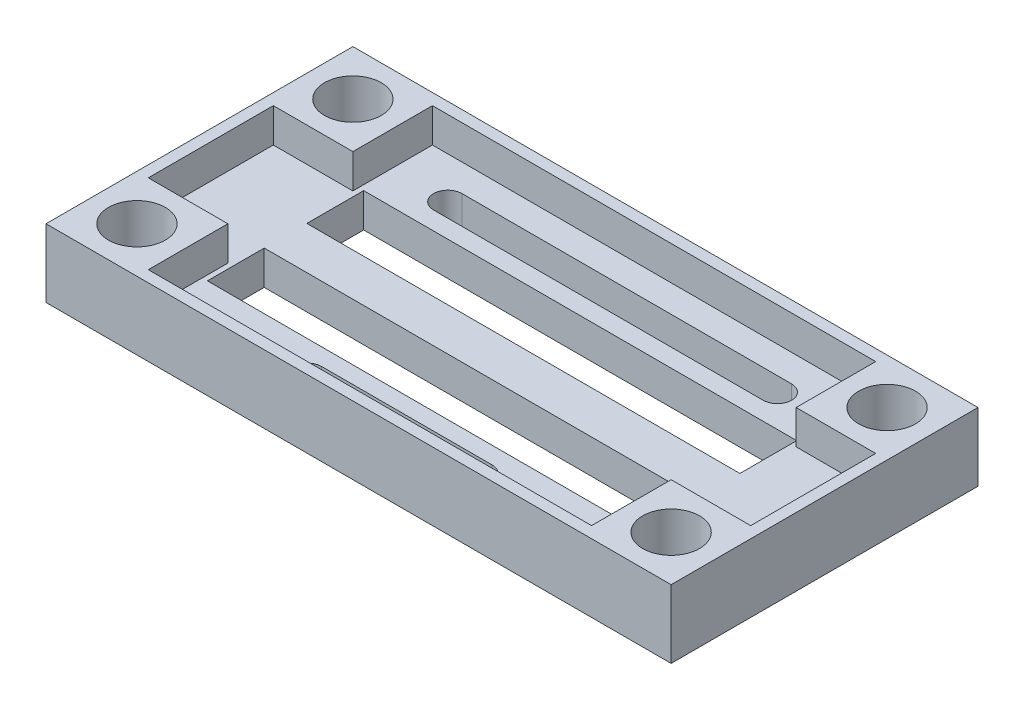
SolidWorks part; units mm, degrees
ref_plane "Front Plane" through (0, 0, 0) normal (0, 0, 1) x (1, 0, 0)
ref_plane "Top Plane" through (0, 0, 0) normal (0, 1, 0) x (1, 0, 0)
ref_plane "Right Plane" through (0, 0, 0) normal (1, 0, 0) x (0, 0, -1)
sketch "Sketch1" plane through (0, 0, 0) normal (0, 1, 0) x (1, 0, 0)
  line L0 (-19.05, -2.75) -> (19.05, -2.75)
  line L9 (27.5, -13.5) -> (-27.5, -13.5)
  line L10 (27.5, -13.5) -> (27.5, 13.5)
  line L11 (27.5, 13.5) -> (-27.5, 13.5)
  line L20 (-27.5, -13.5) -> (-27.5, 13.5)
  line L21 (27.5, -13.5) -> (-27.5, 13.5) construction
  line L22 (27.5, 13.5) -> (-27.5, -13.5) construction
  line L23 (-19.05, 6) -> (19.05, 6)
  line L24 (-19.05, 6) -> (-19.05, 1)
  line L25 (-19.05, 1) -> (19.05, 1)
  line L26 (19.05, 6) -> (19.05, 1)
  line L27 (-19.05, -2.75) -> (-19.05, -7.75)
  line L28 (-19.05, -7.75) -> (19.05, -7.75)
  line L29 (19.05, -2.75) -> (19.05, -7.75)
  point P0 (0, 0)
  point P10 (0, 6)
  point P11 (0, 13.5)
  point P15 (0, -2.75)
  dimension "D2" = 55
  dimension "D1" = 27
  dimension "D3" = 38.1
  dimension "D4" = 7.5
  dimension "D5" = 5
  dimension "D6" = 3.75
extrude "Bottom Base" add sketch "Sketch1" along normal blind 3
sketch "Sketch3" plane through (0, 3, 0) normal (0, 1, 0) x (1, 0, 0)
  line L0 (-27.5, 8.85) -> (27.5, 8.85) construction
  line L1 (27.5, 13.5) -> (-27.5, 13.5) construction
  line L3 (-14.5, 10.1) -> (14.5, 10.1) construction
  line L4 (19.05, 6) -> (-19.05, 6) construction
  line L5 (-14.5, 8.85) -> (14.5, 8.85) construction
  line L6 (-14.5, 10.1) -> (14.5, 10.1)
  line L7 (-14.5, 7.6) -> (14.5, 7.6)
  line L8 (-27.5, 13.5) -> (-27.5, -13.5) construction
  line L9 (27.5, -13.5) -> (27.5, 13.5) construction
  circle A0 centre (-14.5, 8.85) radius 1.09 construction
  circle A2 centre (-14.5, 8.85) radius 1.25 construction
  circle A3 centre (14.5, 8.85) radius 1.25 construction
  arc A6 (-14.5, 10.1) -> (-14.5, 7.6) centre (-14.5, 8.85) ccw
  arc A7 (14.5, 7.6) -> (14.5, 10.1) centre (14.5, 8.85) ccw
  point P21 (0, 6)
  point P22 (0, 10.1)
  point P25 (0, 8.85)
  dimension "D2" = 2.5
  dimension "D5" = 1.25
  dimension "D1" = 29
  dimension "D6" = 4.65
extrude "Sensor Mounting Holes" cut sketch "Sketch3" against normal blind 3
sketch "Sketch4" plane through (0, 3, 0) normal (0, 1, 0) x (1, 0, 0)
  line L0 (27.5, -13.5) -> (27.5, 13.5) construction
  line L1 (27.5, 13.5) -> (-27.5, 13.5) construction
  line L2 (-27.5, -13.5) -> (27.5, -13.5) construction
  line L3 (-27.5, 13.5) -> (-27.5, -13.5) construction
  line L4 (27.5, -13.5) -> (27.5, 13.5)
  line L5 (27.5, 13.5) -> (-27.5, 13.5)
  line L6 (-27.5, -13.5) -> (27.5, -13.5)
  line L7 (-27.5, 13.5) -> (-27.5, -13.5)
  line L8 (26.5, -12.5) -> (26.5, 12.5)
  line L9 (26.5, 12.5) -> (-26.5, 12.5)
  line L10 (-26.5, 12.5) -> (-26.5, -12.5)
  line L11 (-26.5, -12.5) -> (26.5, -12.5)
  line L12 (0, -13.5) -> (0, 13.5) construction
  line L13 (-26.5, -12.5) -> (-19.5, -12.5)
  line L14 (-26.5, -12.5) -> (-26.5, -5.5)
  line L15 (-26.5, -5.5) -> (-19.5, -5.5)
  line L16 (-19.5, -12.5) -> (-19.5, -5.5)
  line L29 (27.5, 0) -> (-27.5, 0) construction
  line L30 (26.5, -5.5) -> (19.5, -5.5)
  line L31 (19.5, -12.5) -> (19.5, -5.5)
  line L32 (26.5, -12.5) -> (19.5, -12.5)
  line L33 (26.5, -12.5) -> (26.5, -5.5)
  line L34 (26.5, 12.5) -> (19.5, 12.5)
  line L35 (19.5, 12.5) -> (19.5, 5.5)
  line L36 (26.5, 5.5) -> (19.5, 5.5)
  line L37 (26.5, 12.5) -> (26.5, 5.5)
  line L38 (-26.5, 5.5) -> (-19.5, 5.5)
  line L39 (-19.5, 12.5) -> (-19.5, 5.5)
  line L40 (-26.5, 12.5) -> (-19.5, 12.5)
  line L41 (-26.5, 12.5) -> (-26.5, 5.5)
  point P14 (0, 0)
  point P17 (0, 0)
  line M13 (-27.5, 13.5) -> (-27.5, -13.5)
  line M14 (-27.5, -13.5) -> (27.5, -13.5)
  line M15 (27.5, -13.5) -> (27.5, 13.5)
  line M16 (27.5, 13.5) -> (-27.5, 13.5)
  dimension "D2" = 7
  dimension "D1" = 1
extrude "Outer Rim" add sketch "Sketch4" along normal blind 3 contours L39 L9 L10 L38 | L11 L16 L15 L10 | L31 L11 L8 L30 | L36 L8 L9 L35 | L11 L10 L9 L8 M16 M13 M14 M15
sketch "Sketch6" plane through (0, 6, 0) normal (0, 1, 0) x (1, 0, 0)
  line L0 (-26.5, -5.5) -> (-19.5, -5.5) construction
  line L1 (-19.5, 5.5) -> (-27.5, 5.5) construction
  line L2 (-19.5, 5.5) -> (-19.5, 13.5) construction
  line L3 (-19.5, 13.5) -> (-27.5, 13.5) construction
  line L4 (-27.5, 5.5) -> (-27.5, 13.5) construction
  line L5 (-19.5, 5.5) -> (-27.5, 13.5) construction
  line L6 (-19.5, 13.5) -> (-27.5, 5.5) construction
  line L7 (-19.5, -13.5) -> (-27.5, -13.5) construction
  line L8 (-19.5, -13.5) -> (-19.5, -5.5) construction
  line L9 (-19.5, -5.5) -> (-27.5, -5.5) construction
  line L10 (-27.5, -13.5) -> (-27.5, -5.5) construction
  line L11 (-19.5, -13.5) -> (-27.5, -5.5) construction
  line L12 (-19.5, -5.5) -> (-27.5, -13.5) construction
  line L17 (-26.5, -5.5) -> (-19.5, -5.5) construction
  line L18 (19.5, -12.5) -> (19.5, -5.5) construction
  line L23 (27.5, 5.5) -> (19.5, 5.5) construction
  line L24 (27.5, 5.5) -> (27.5, 13.5) construction
  line L25 (27.5, 13.5) -> (19.5, 13.5) construction
  line L26 (19.5, 5.5) -> (19.5, 13.5) construction
  line L27 (27.5, 5.5) -> (19.5, 13.5) construction
  line L28 (27.5, 13.5) -> (19.5, 5.5) construction
  line L29 (27.5, -13.5) -> (19.5, -13.5) construction
  line L30 (27.5, -13.5) -> (27.5, -5.5) construction
  line L31 (27.5, -5.5) -> (19.5, -5.5) construction
  line L32 (19.5, -13.5) -> (19.5, -5.5) construction
  line L33 (27.5, -13.5) -> (19.5, -5.5) construction
  line L34 (27.5, -5.5) -> (19.5, -13.5) construction
  line L35 (-19.5, -12.5) -> (-19.5, -5.5) construction
  line L36 (-19.5, -12.5) -> (-19.5, -5.5) construction
  line L37 (27.5, -13.5) -> (27.5, 13.5) construction
  point P0 (-23.5, 9.5)
  point P5 (-23.5, -9.5)
  point P10 (23.5, -9.5)
  point P16 (23.5, 9.5)
hole_wizard "M4 bolt holes" positions "Sketch7" profile "Sketch8" hole size "Ø5.0" standard "ANSI Metric" end condition through all
sketch "Sketch7" plane through (0, 6, 0) normal (0, 1, 0) x (1, 0, 0)
  line L0 (-19.5, -13.5) -> (-27.5, -5.5) construction
  point P0 (-23.5, 9.5)
  point P3 (-23.5, -9.5)
  point P7 (23.5, 9.5)
  point P10 (23.5, -9.5)
sketch "Sketch8" plane through (-23.5, 6, -9.5) normal (1, 0, 0) x (0, 0, 1)
  line L0 (0, 0) -> (0, 6)
  line L1 (0, 6) -> (2.5, 6)
  line L2 (2.5, 6) -> (2.5, 0)
  line L5 (2.5, 0) -> (0, 0)
  line L11 (0, -6.35) -> (0, 107.95) construction
  dimension "Thru Hole Dia." = 5
  dimension "Thru Hole Depth" = 6
sketch "Sketch10" plane through (0, 0, 0) normal (0, -1, 0) x (1, 0, 0)
  line L0 (-27.5, -3.5) -> (27.5, -3.5) construction
  line L1 (-27.5, -13.5) -> (-27.5, 13.5) construction
  line L2 (27.5, 13.5) -> (27.5, -13.5) construction
  line L3 (-19.05, -6) -> (-19.05, -1) construction
  point P8 (-19.05, -3.5)
sketch "Sketch11" plane through (0, 3, 0) normal (0, 1, 0) x (1, 0, 0)
  line L0 (-7.5, -10.5) -> (7.5, -10.5) construction
  line L1 (-7.5, -9.25) -> (7.5, -9.25)
  line L2 (-7.5, -11.75) -> (7.5, -11.75)
  line L3 (-19.5, -12.5) -> (19.5, -12.5) construction
  arc A0 (-7.5, -9.25) -> (-7.5, -11.75) centre (-7.5, -10.5) ccw
  arc A1 (7.5, -11.75) -> (7.5, -9.25) centre (7.5, -10.5) ccw
  arc A2 (-14.5, 10.1) -> (-14.5, 7.6) centre (-14.5, 8.85) ccw construction
  point P2 (0, -10.5)
  dimension "D1" = 2
  dimension "D2" = 15
extrude "backwards sensor" cut sketch "Sketch11" against normal up to surface (3 mm away) up to face at (-23.5, 0, -7)
